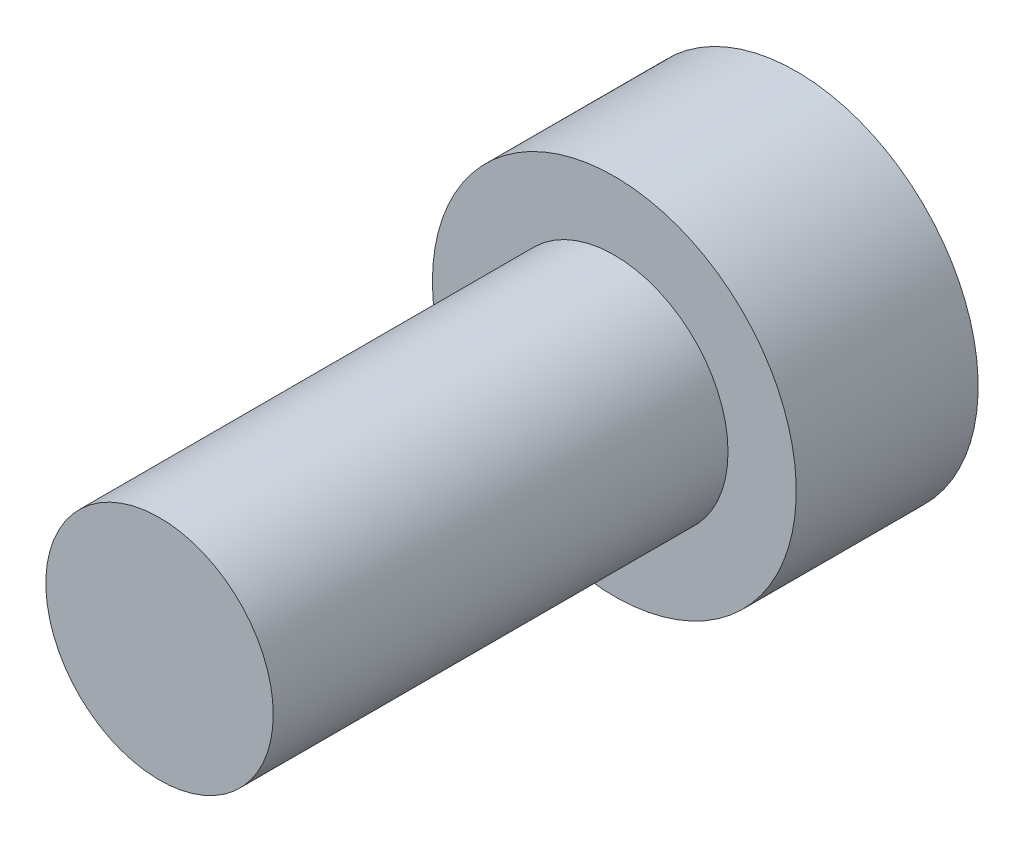
SolidWorks part; units mm, degrees
ref_plane "Front Plane" through (0, 0, 0) normal (0, 0, 1) x (1, 0, 0)
ref_plane "Top Plane" through (0, 0, 0) normal (0, 1, 0) x (1, 0, 0)
ref_plane "Right Plane" through (0, 0, 0) normal (1, 0, 0) x (0, 0, -1)
sketch "Sketch1" plane through (0, 0, 0) normal (0, 0, 1) x (1, 0, 0)
  circle A0 centre (0, 0) radius 2.5
extrude "Boss-Extrude1" add sketch "Sketch1" along normal blind 10 contours A0
cosmetic thread "Cosmetic Thread1" parameters "D1"=8, "D2"=4.11
sketch "Sketch2" plane through (0, 0, 0) normal (0, 0, -1) x (-1, 0, 0)
  circle A0 centre (0, 0) radius 4
  dimension "D1" = 8
extrude "Boss-Extrude2" add sketch "Sketch2" along normal blind 4
sketch "Sketch3" plane through (0, 0, -4) normal (0, 0, -1) x (-1, 0, 0)
  line L1 (1.7321, -3) -> (3.4641, 0)
  line L2 (3.4641, 0) -> (1.7321, 3)
  line L3 (1.7321, 3) -> (-1.7321, 3)
  line L4 (-1.7321, 3) -> (-3.4641, 0)
  line L5 (-3.4641, 0) -> (-1.7321, -3)
  line L6 (-1.7321, -3) -> (1.7321, -3)
  circle A0 centre (0, 0) radius 3 construction
  point P1 (0, 0)
  dimension "D1" = 6
extrude "Cut-Extrude1" cut sketch "Sketch3" against normal blind 3 contours L4 L5 L6 L1 L2 L3
